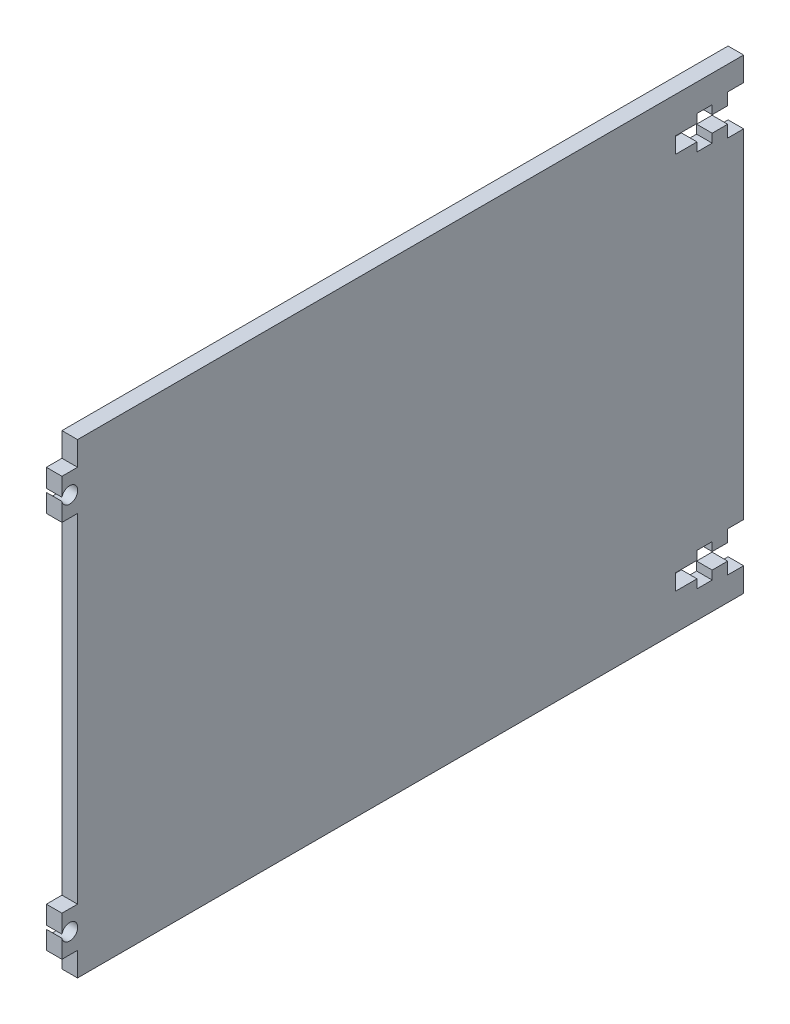
SolidWorks part; units mm, degrees
ref_plane "Front Plane" through (0, 0, 0) normal (0, 0, 1) x (1, 0, 0)
ref_plane "Top Plane" through (0, 0, 0) normal (0, 1, 0) x (1, 0, 0)
ref_plane "Right Plane" through (0, 0, 0) normal (1, 0, 0) x (0, 0, -1)
sketch "Sketch2" plane through (0, 0, 0) normal (1, 0, 0) x (0, 0, -1)
  line L0 (-94.3113, 35.295) -> (-56.9475, 35.295) construction
  line L1 (-73.0099, 43.677) -> (53.9901, 43.677)
  line L2 (-73.0099, 43.677) -> (-73.0099, 39.105)
  line L3 (-73.0099, -45.223) -> (53.9901, -45.223)
  line L4 (53.9901, 43.677) -> (53.9901, 39.105)
  line L5 (-98.9496, -0.773) -> (-45.6096, -0.773) construction
  line L6 (-75.9817, -36.5024) -> (-75.9817, -33.031)
  line L7 (-73.0099, 39.105) -> (-75.9817, 39.105)
  line L8 (-75.9817, 39.105) -> (-75.9817, 35.6336)
  line L9 (-75.9817, 31.485) -> (-73.0099, 31.485)
  line L10 (-73.0099, 31.485) -> (-73.0099, -33.031)
  line L11 (-75.9817, -33.031) -> (-73.0099, -33.031)
  line L12 (-75.9817, -40.651) -> (-75.9817, -37.1797)
  line L13 (-73.0099, -40.651) -> (-75.9817, -40.651)
  line L14 (-73.0099, -40.651) -> (-73.0099, -45.223)
  line L15 (-75.9817, 34.9563) -> (-75.9817, 31.485)
  line L16 (53.9901, 39.105) -> (50.9421, 39.105)
  line L17 (50.9421, 39.105) -> (50.9421, 36.819)
  line L18 (50.9421, 36.819) -> (47.9891, 36.819)
  line L19 (47.9891, 36.819) -> (47.9891, 38.47)
  line L20 (47.9891, 38.47) -> (45.1001, 38.47)
  line L21 (45.1001, 38.47) -> (45.1001, 36.819)
  line L22 (45.1001, 36.819) -> (41.0361, 36.819)
  line L23 (41.0361, 36.819) -> (41.0361, 33.771)
  line L24 (41.0361, 33.771) -> (45.1001, 33.771)
  line L25 (45.1001, 33.771) -> (45.1001, 32.12)
  line L26 (45.1001, 32.12) -> (47.9891, 32.12)
  line L27 (47.9891, 32.12) -> (47.9891, 33.771)
  line L28 (47.9891, 33.771) -> (50.9421, 33.771)
  line L29 (50.9421, 33.771) -> (50.9421, 31.485)
  line L30 (50.9421, 31.485) -> (53.9901, 31.485)
  line L31 (53.9901, 35.295) -> (24.8822, 35.295) construction
  line L32 (46.5446, 38.47) -> (46.5446, 32.12) construction
  line L33 (52.4661, 39.105) -> (52.4661, 31.485) construction
  line L34 (53.9901, 31.485) -> (53.9901, -33.031)
  line L35 (52.4661, -40.651) -> (52.4661, -33.031) construction
  line L36 (46.5446, -40.016) -> (46.5446, -33.666) construction
  line L37 (50.9421, -33.031) -> (53.9901, -33.031)
  line L38 (50.9421, -35.317) -> (50.9421, -33.031)
  line L39 (47.9891, -35.317) -> (50.9421, -35.317)
  line L40 (47.9891, -33.666) -> (47.9891, -35.317)
  line L41 (45.1001, -33.666) -> (47.9891, -33.666)
  line L42 (45.1001, -35.317) -> (45.1001, -33.666)
  line L43 (41.0361, -35.317) -> (45.1001, -35.317)
  line L44 (41.0361, -38.365) -> (41.0361, -35.317)
  line L45 (45.1001, -38.365) -> (41.0361, -38.365)
  line L46 (45.1001, -40.016) -> (45.1001, -38.365)
  line L47 (47.9891, -40.016) -> (45.1001, -40.016)
  line L48 (47.9891, -38.365) -> (47.9891, -40.016)
  line L49 (50.9421, -38.365) -> (47.9891, -38.365)
  line L50 (50.9421, -40.651) -> (50.9421, -38.365)
  line L51 (53.9901, -40.651) -> (50.9421, -40.651)
  line L52 (53.9901, -40.651) -> (53.9901, -45.223)
  arc A0 (-75.9817, 34.9563) -> (-75.9817, 35.6336) centre (-74.4958, 35.295) ccw
  arc A1 (-75.9817, -36.5024) -> (-75.9817, -37.1797) centre (-74.4958, -36.841) cw
  point P40 (52.4661, 31.485)
  point P41 (41.0361, 35.295)
  point P44 (46.5446, 35.295)
  point P47 (52.4661, 35.295)
  dimension "D7" = 3.048
  dimension "D1" = 88.9
  dimension "D2" = 127
  dimension "D3" = 8.382
  dimension "D4" = 7.62
  dimension "D5" = 2.9718
  dimension "D6" = 1.4859
  dimension "D9" = 3.048
  dimension "D10" = 7.62
  dimension "D11" = 12.954
  dimension "D12" = 8.89
  dimension "D13" = 6.35
  dimension "D14" = 3.048
extrude "Boss-Extrude1" add sketch "Sketch2" along normal blind 2.9718
